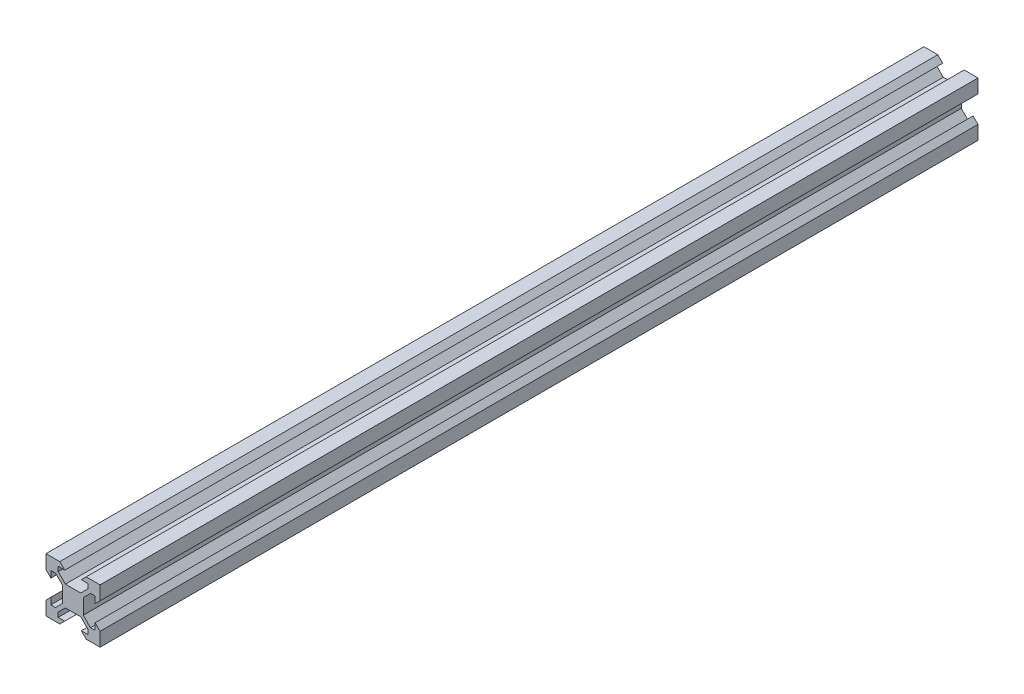
SolidWorks part; units mm, degrees
ref_plane "Front Plane" through (0, 0, 0) normal (0, 0, 1) x (1, 0, 0)
ref_plane "Top Plane" through (0, 0, 0) normal (0, 1, 0) x (1, 0, 0)
ref_plane "Right Plane" through (0, 0, 0) normal (1, 0, 0) x (0, 0, -1)
sketch "Sketch1" plane through (0, 0, 0) normal (0, 0, 1) x (1, 0, 0)
  line L1 (0, 0) -> (20, 0)
  line L2 (0, 0) -> (0, 20)
  line L3 (0, 20) -> (20, 20)
  line L4 (20, 0) -> (20, 20)
  line L5 (0, 0) -> (20, 20) construction
  line L6 (0, 20) -> (20, 0) construction
  point P4 (10, 10)
  dimension "D1" = 20
  dimension "D2" = 20
extrude "Boss-Extrude1" add sketch "Sketch1" along normal blind 324.8
sketch "Sketch2" plane through (0, 0, 324.8) normal (0, 0, 1) x (1, 0, 0)
  line L4 (0, 0) -> (20, 20) construction
  line L5 (4.5, 18.18) -> (6.94, 18.18)
  line L6 (4.5, 16.4758) -> (4.5, 18.18)
  line L15 (7.1658, 13.81) -> (4.5, 16.4758)
  line L17 (12.8342, 13.81) -> (7.1658, 13.81)
  line L27 (15.5, 16.4758) -> (12.8342, 13.81)
  line L29 (15.5, 18.18) -> (15.5, 16.4758)
  line L31 (13.06, 18.18) -> (15.5, 18.18)
  line L33 (14.88, 20) -> (5.12, 20)
  line L35 (6.94, 18.18) -> (5.12, 20)
  line L54 (14.88, 20) -> (13.06, 18.18)
  line L56 (14.88, 0) -> (13.06, 1.82)
  line L57 (6.94, 1.82) -> (5.12, 0)
  line L58 (14.88, 0) -> (5.12, 0)
  line L68 (13.06, 1.82) -> (15.5, 1.82)
  line L71 (15.5, 1.82) -> (15.5, 3.5242)
  line L81 (15.5, 3.5242) -> (12.8342, 6.19)
  line L82 (12.8342, 6.19) -> (7.1658, 6.19)
  line L83 (7.1658, 6.19) -> (4.5, 3.5242)
  line L84 (4.5, 3.5242) -> (4.5, 1.82)
  line L85 (4.5, 1.82) -> (6.94, 1.82)
  line L136 (20, 0) -> (10, 0) construction
  line L137 (0, 0) -> (20, 0) construction
  line L186 (1.82, 4.5) -> (1.82, 6.94)
  line L187 (3.5242, 4.5) -> (1.82, 4.5)
  line L188 (6.19, 7.1658) -> (3.5242, 4.5)
  line L189 (6.19, 12.8342) -> (6.19, 7.1658)
  line L190 (3.5242, 15.5) -> (6.19, 12.8342)
  line L191 (1.82, 15.5) -> (3.5242, 15.5)
  line L192 (1.82, 13.06) -> (1.82, 15.5)
  line L193 (0, 14.88) -> (0, 5.12)
  line L194 (1.82, 6.94) -> (0, 5.12)
  line L195 (0, 14.88) -> (1.82, 13.06)
  line L203 (20, 14.88) -> (18.18, 13.06)
  line L205 (18.18, 6.94) -> (20, 5.12)
  line L206 (20, 14.88) -> (20, 5.12)
  line L207 (18.18, 13.06) -> (18.18, 15.5)
  line L208 (18.18, 15.5) -> (16.4758, 15.5)
  line L209 (16.4758, 15.5) -> (13.81, 12.8342)
  line L210 (13.81, 12.8342) -> (13.81, 7.1658)
  line L211 (13.81, 7.1658) -> (16.4758, 4.5)
  line L212 (16.4758, 4.5) -> (18.18, 4.5)
  line L213 (18.18, 4.5) -> (18.18, 6.94)
extrude "Cut-Extrude1" cut sketch "Sketch2" against normal through all
